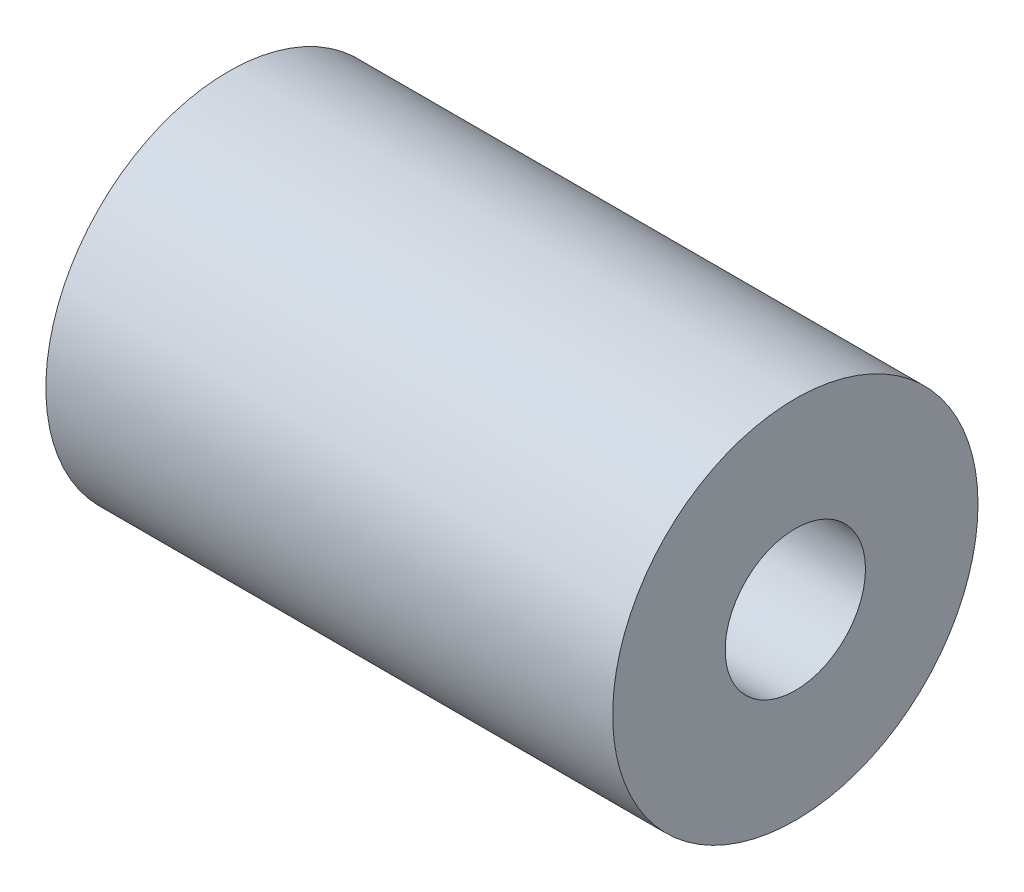
SolidWorks part; units mm, degrees
ref_plane "Front Plane" through (0, 0, 0) normal (0, 0, 1) x (1, 0, 0)
ref_plane "Top Plane" through (0, 0, 0) normal (0, 1, 0) x (1, 0, 0)
ref_plane "Right Plane" through (0, 0, 0) normal (1, 0, 0) x (0, 0, -1)
sketch "Sketch1" plane through (0, 0, 0) normal (1, 0, 0) x (0, 0, -1)
  circle A0 centre (0, 0) radius 8.2677
  circle A1 centre (0, 0) radius 3.175
  dimension "D1" = 16.5354
  dimension "D2" = 6.35
extrude "Boss-Extrude1" add sketch "Sketch1" along normal mid plane 25.654
